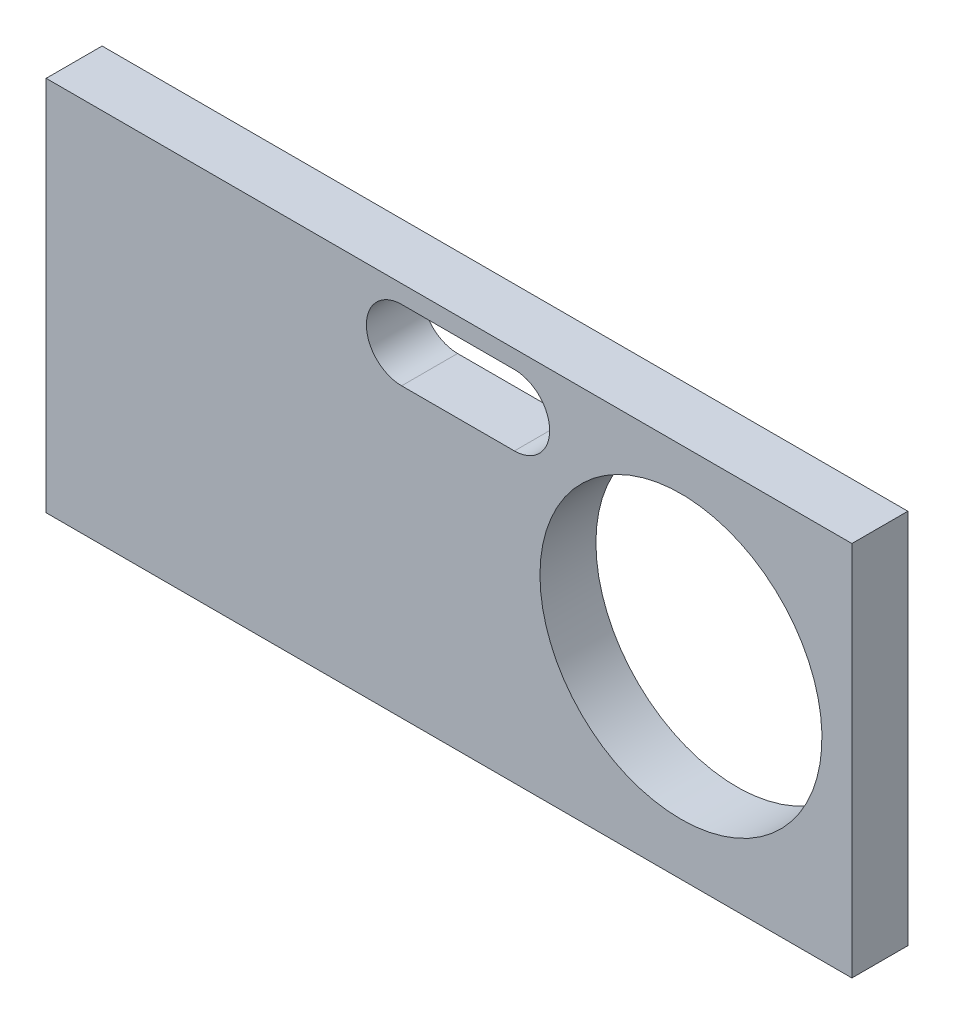
SolidWorks part; units mm, degrees
ref_plane "Front Plane" through (0, 0, 0) normal (0, 0, 1) x (1, 0, 0)
ref_plane "Top Plane" through (0, 0, 0) normal (0, 1, 0) x (1, 0, 0)
ref_plane "Right Plane" through (0, 0, 0) normal (1, 0, 0) x (0, 0, -1)
sketch "Sketch1" plane through (0, 0, 0) normal (0, 1, 0) x (1, 0, 0)
  line L1 (-22.86, -10.16) -> (22.86, -10.16)
  line L2 (-22.86, -10.16) -> (-22.86, 10.16)
  line L3 (-22.86, 10.16) -> (22.86, 10.16)
  line L4 (22.86, -10.16) -> (22.86, 10.16)
  line L5 (-22.86, -10.16) -> (22.86, 10.16) construction
  line L6 (-22.86, 10.16) -> (22.86, -10.16) construction
  point P0 (0, 0)
  dimension "D1" = 20.32
  dimension "D2" = 45.72
extrude "Boss-Extrude1" add sketch "Sketch1" along normal blind 3.175
sketch "Sketch2" plane through (22.86, 0, 0) normal (1, 0, 0) x (0, 0, -1)
  line L0 (10.16, 3.175) -> (10.16, 44.958)
  line L1 (10.16, 44.958) -> (6.985, 44.958)
  line L2 (6.985, 44.958) -> (6.985, 3.175)
  line L3 (-10.16, 3.175) -> (10.16, 3.175) construction
  line L4 (6.985, 3.175) -> (10.16, 3.175)
  dimension "D1" = 44.958
  dimension "D2" = 3.175
extrude "Boss-Extrude2" add sketch "Sketch2" against normal up to vertex (45.72 mm away)
sketch "Sketch3" plane through (22.86, 0, 0) normal (1, 0, 0) x (0, 0, -1)
  line L0 (-10.16, 3.175) -> (6.985, 23.6076)
  line L1 (6.985, 44.958) -> (6.985, 3.175) construction
  line L2 (-10.16, 3.175) -> (6.985, 3.175) construction
  dimension "D1" = 50
sketch "Sketch4" plane through (0, 3.175, 0) normal (0, 1, 0) x (1, 0, 0)
  line L0 (-22.86, 6.985) -> (22.86, 6.985) construction
  line L1 (-22.86, -10.16) -> (-20.828, -10.16)
  line L2 (-22.86, -10.16) -> (-22.86, 6.985)
  line L3 (-22.86, 6.985) -> (-20.828, 6.985)
  line L4 (-20.828, -10.16) -> (-20.828, 6.985)
  line L5 (-22.86, 6.985) -> (22.86, 6.985) construction
  line L6 (22.86, -10.16) -> (20.828, -10.16)
  line L7 (22.86, -10.16) -> (22.86, 6.985)
  line L8 (22.86, 6.985) -> (20.828, 6.985)
  line L9 (20.828, -10.16) -> (20.828, 6.985)
  dimension "D1" = 2.032
  dimension "D2" = 2.032
sweep "Sweep1" add profiles "Sketch4" path "Sketch3"
sketch "Sketch5" plane through (0, 0, -10.16) normal (0, 0, -1) x (-1, 0, 0)
  line L0 (-3.71, 43.933) -> (2.69, 43.933)
  line L1 (-3.71, 39.933) -> (-3.71, 40.233) construction
  line L2 (2.69, 40.233) -> (2.69, 39.933) construction
  line L3 (-3.71, 39.933) -> (2.69, 39.933)
  circle A0 centre (-13.16, 34.558) radius 8
  arc A2 (-3.71, 43.933) -> (-3.71, 39.933) centre (-3.71, 41.933) ccw
  arc A3 (2.69, 43.933) -> (2.69, 39.933) centre (2.69, 41.933) cw
extrude "Cut-Extrude1" cut sketch "Sketch5" against normal through all
sketch "Sketch6" plane through (0, 0, 0) normal (0, -1, 0) x (1, 0, 0)
  line L1 (22.86, 10.16) -> (22.86, -10.16) construction
  line L2 (-22.86, 10.16) -> (22.86, 10.16) construction
  circle A0 centre (-15.5649, -0.1904) radius 2.2225
  circle A1 centre (15.5575, -0.1904) radius 2.2225
  point P6 (-17.7795, -0.0034)
  point P7 (-15.5426, 2.032)
  point P8 (17.78, -0.1904)
  point P9 (15.5575, 2.0321)
  dimension "D1" = 4.445
  dimension "D4" = 35.5595
  dimension "D2" = 8.128
  dimension "D3" = 5.08
extrude "Cut-Extrude2" cut sketch "Sketch6" against normal through all
sketch "Sketch7" plane through (22.86, 0, 0) normal (1, 0, 0) x (0, 0, -1)
  line L0 (6.985, 23.6076) -> (-24.3015, 23.6076)
  line L1 (-24.3015, 23.6076) -> (-24.3015, -6.9679)
  line L2 (-24.3015, -6.9679) -> (28.3046, -6.9679)
  line L4 (6.985, 23.6076) -> (28.3046, 23.6076)
  line L5 (28.3046, 23.6076) -> (28.3046, -6.9679)
extrude "Cut-Extrude3" cut sketch "Sketch7" against normal through all
